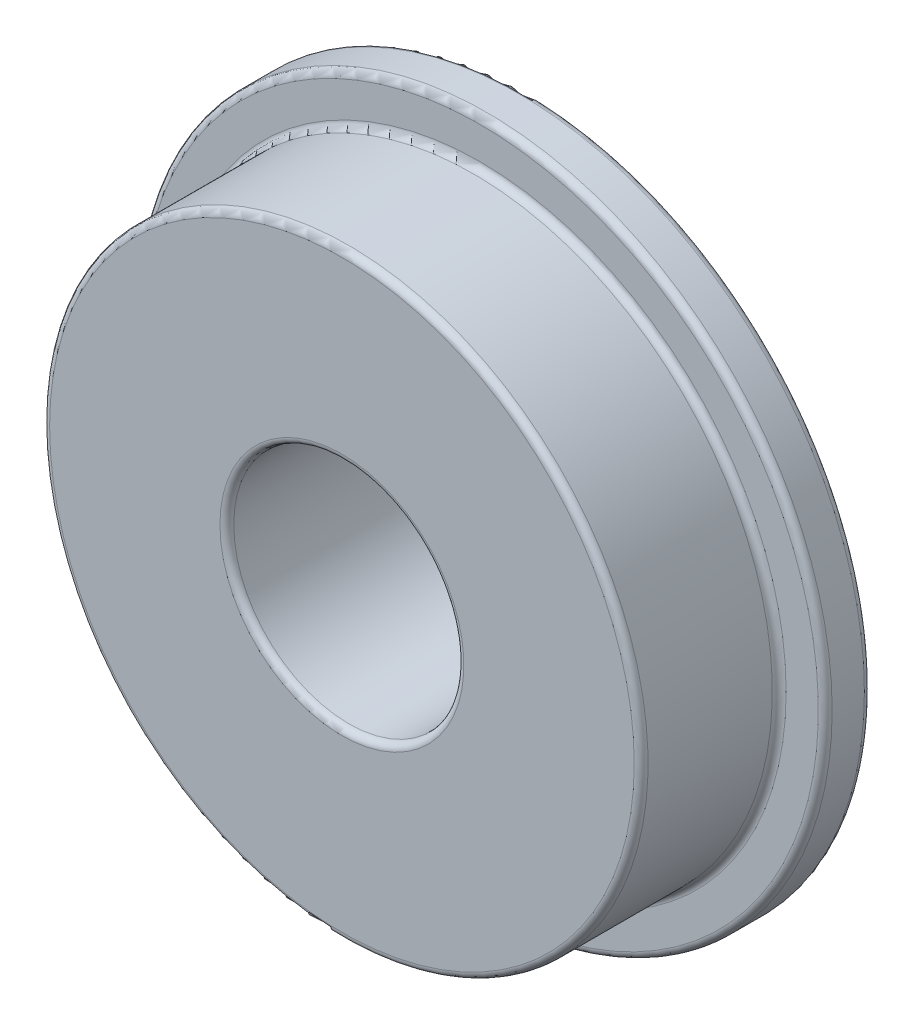
SolidWorks part; units mm, degrees
material "Chrome Stainless Steel"
ref_plane "Front Plane" through (0, 0, 0) normal (0, 0, 1) x (1, 0, 0)
ref_plane "Top Plane" through (0, 0, 0) normal (0, 1, 0) x (1, 0, 0)
ref_plane "Right Plane" through (0, 0, 0) normal (1, 0, 0) x (0, 0, -1)
sketch "Sketch1" plane through (0, 0, 0) normal (1, 0, 0) x (0, 0, -1)
  line L0 (0, 0) -> (-17.0468, 0) construction
  line L1 (4, 2.65) -> (4, 7.35)
  line L2 (3.85, 7.5) -> (3.15, 7.5)
  line L3 (3, 7.35) -> (3, 6.65)
  line L4 (2.85, 6.5) -> (0.15, 6.5)
  line L5 (0, 6.35) -> (0, 2.65)
  line L6 (0.15, 2.5) -> (3.85, 2.5)
  arc A0 (0.15, 2.5) -> (0, 2.65) centre (0.15, 2.65) cw
  arc A1 (3.85, 2.5) -> (4, 2.65) centre (3.85, 2.65) ccw
  arc A2 (0.15, 6.5) -> (0, 6.35) centre (0.15, 6.35) ccw
  arc A3 (3, 6.65) -> (2.85, 6.5) centre (2.85, 6.65) cw
  arc A4 (4, 7.35) -> (3.85, 7.5) centre (3.85, 7.35) ccw
  arc A5 (3.15, 7.5) -> (3, 7.35) centre (3.15, 7.35) ccw
  dimension "D6" = 0.15
  dimension "D1" = 2.5
  dimension "D2" = 6.5
  dimension "D3" = 4
  dimension "D4" = 1
  dimension "D5" = 7.5
revolve "Revolve1" add sketch "Sketch1" angle 360 about L0
